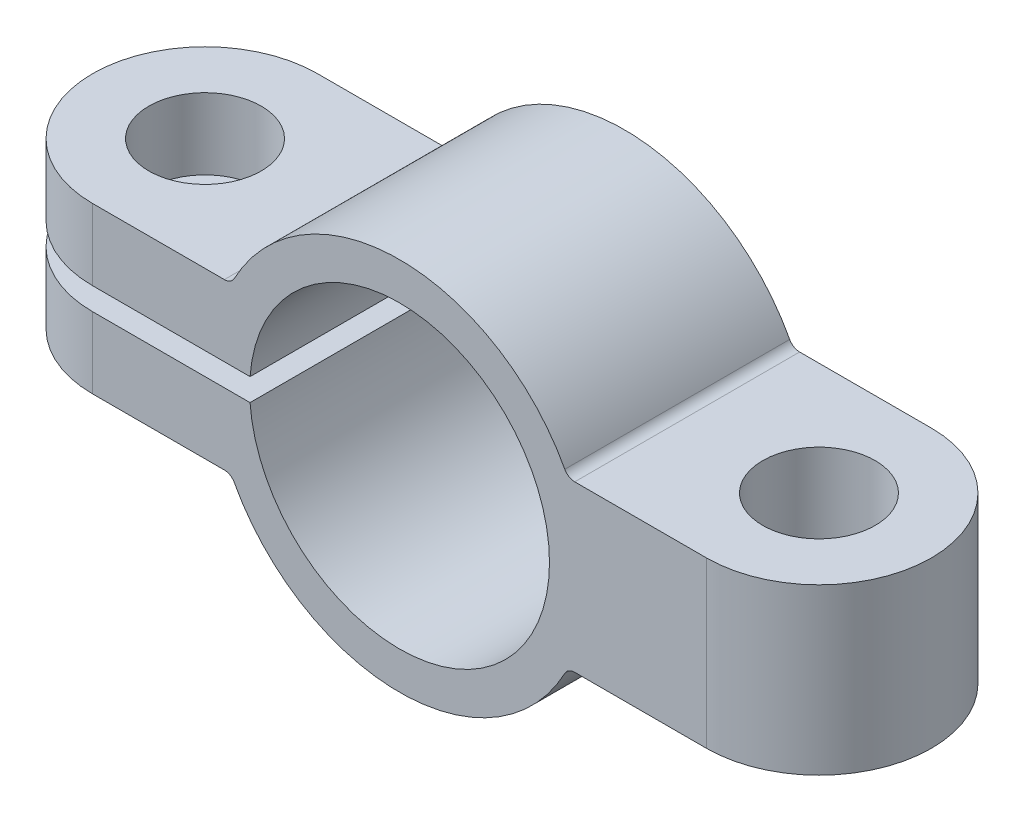
SolidWorks part; units mm, degrees
ref_plane "前视基准面" through (0, 0, 0) normal (0, 0, 1) x (1, 0, 0)
ref_plane "上视基准面" through (0, 0, 0) normal (0, 1, 0) x (1, 0, 0)
ref_plane "右视基准面" through (0, 0, 0) normal (1, 0, 0) x (0, 0, -1)
sketch "草图2" plane through (0, 0, 0) normal (0, 0, 1) x (1, 0, 0)
  line L0 (-10.1446, 0) -> (-4, 0) construction
  line L1 (-11.19, 0.3) -> (-11.19, 2.2)
  line L2 (-11.19, 2.2) -> (-4.49, 2.2)
  line L3 (4.49, 2.2) -> (11.19, 2.2)
  line L4 (11.19, 2.2) -> (11.19, 0)
  line L5 (11.19, 0) -> (4, 0)
  line L6 (0, -1.561) -> (0, 1.9942) construction
  line L7 (4, 0) -> (5.5563, 0) construction
  line L8 (-11.19, 0.3) -> (-3.9887, 0.3)
  arc A0 (-4.49, 2.2) -> (4.49, 2.2) centre (0, 0) cw
  arc A1 (4, 0) -> (-3.9887, 0.3) centre (0, 0) ccw
  dimension "D3" = 1
  dimension "D2" = 4
  dimension "D1" = 2.2
  dimension "D4" = 6.7
  dimension "D5" = 0.3
extrude "凸台-拉伸1" add sketch "草图2" along normal blind 6
mirror "镜向2" about plane through (0, 0, 0) normal (0, 1, 0) of "凸台-拉伸1"
sketch "草图3" plane through (0, 2.2, 0) normal (0, 1, 0) x (1, 0, 0)
  line L0 (-4.49, 0) -> (-11.19, 0) construction
  line L1 (-11.19, -6) -> (-11.19, 0) construction
  line L2 (-4.49, -6) -> (-11.19, -6) construction
  line L7 (-4.49, 0) -> (-11.19, 0)
  line L8 (-11.19, 0) -> (-11.19, -6)
  line L9 (-11.19, -6) -> (-4.49, -6)
  line L10 (-4.49, -6) -> (-4.49, 0)
  line L11 (-8.19, 0) -> (-11.19, 0)
  line L12 (-11.19, 0) -> (-11.19, -6)
  line L13 (-11.19, -6) -> (-8.19, -6)
  arc A0 (-8.19, 0) -> (-8.19, -6) centre (-8.19, -3) ccw
  line M5 (-4.49, 0) -> (-11.19, 0)
  line M6 (-11.19, 0) -> (-11.19, -6)
  line M7 (-11.19, -6) -> (-4.49, -6)
  dimension "D1" = 0
extrude "切除-拉伸1" cut sketch "草图3" against normal through all contours A0 M5 M6 | A0 L12 M7
mirror "镜向1" about plane through (0, 0, 0) normal (1, 0, 0) of "切除-拉伸1"
sketch "草图4" plane through (0, 2.2, 0) normal (0, 1, 0) x (1, 0, 0)
  line L3 (-8.19, -6) -> (-4.49, -6)
  line L4 (-4.49, -6) -> (-4.49, 0)
  line L5 (-4.49, 0) -> (-8.19, 0)
  line L6 (8.19, 0) -> (4.49, 0)
  line L7 (4.49, 0) -> (4.49, -6)
  line L8 (4.49, -6) -> (8.19, -6)
  circle A0 centre (-8.19, -3) radius 1.5
  arc A1 (-8.19, 0) -> (-8.19, -6) centre (-8.19, -3) ccw
  arc A2 (-8.19, 0) -> (-8.19, -6) centre (-8.19, -3) ccw construction
  circle A3 centre (8.19, -3) radius 1.5
  arc A4 (8.19, -6) -> (8.19, 0) centre (8.19, -3) ccw
  arc A5 (8.19, -6) -> (8.19, 0) centre (8.19, -3) ccw construction
  dimension "D2" = 3
  dimension "D4" = 3
  dimension "D1" = 0
  dimension "D3" = 0
extrude "切除-拉伸2" cut sketch "草图4" against normal through all
fillet "圆角1" radius 0.3 4 edges at (4.49, 2.2, 3) (-4.49, 2.2, 3) (4.49, -2.2, 3) (-4.49, -2.2, 3)
